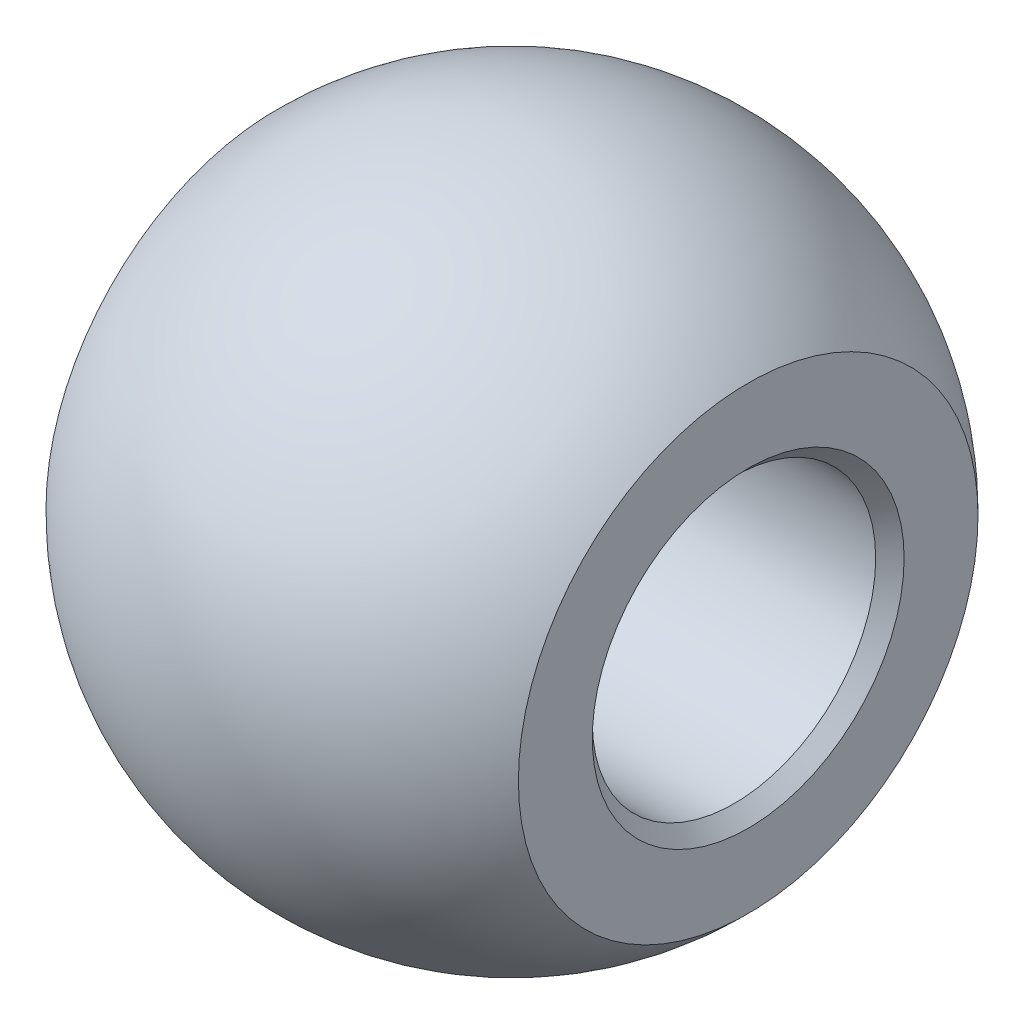
SolidWorks part; units mm, degrees
ref_plane "Front Plane" through (0, 0, 0) normal (0, 0, 1) x (1, 0, 0)
ref_plane "Top Plane" through (0, 0, 0) normal (0, 1, 0) x (1, 0, 0)
ref_plane "Right Plane" through (0, 0, 0) normal (1, 0, 0) x (0, 0, -1)
sketch "Sketch1" plane through (0, 0, 0) normal (0, 0, 1) x (1, 0, 0)
  line L0 (0, 5.5372) -> (0, -5.5372) construction
  line L1 (0, 5.5372) -> (0, -5.5372)
  arc A0 (0, 5.5372) -> (0, -5.5372) centre (0, 0) ccw
  dimension "D1" = 5.5372
revolve "Revolve1" add sketch "Sketch1" angle 360 about L0
sketch "Sketch2" plane through (0, 0, 0) normal (1, 0, 0) x (0, 0, -1)
  circle A0 centre (0, 0) radius 2.3813
  dimension "D1" = 4.7625
extrude "Cut-Extrude1" cut sketch "Sketch2" against normal through all both and the other way through all
sketch "Sketch3" plane through (0, 0, 0) normal (1, 0, 0) x (0, 0, -1)
  circle A0 centre (0, 0) radius 5
  dimension "D1" = 10
extrude "Cut-Extrude2" cut sketch "Sketch3" along normal through all from offset 3.9688
mirror "Mirror1" about plane through (0, 0, 0) normal (1, 0, 0) of "Cut-Extrude2"
chamfer "Chamfer1" distance 0.2388 angle 45 2 edges at (-3.9688, 0, 2.3813) (3.9687, 0, -2.3813)
